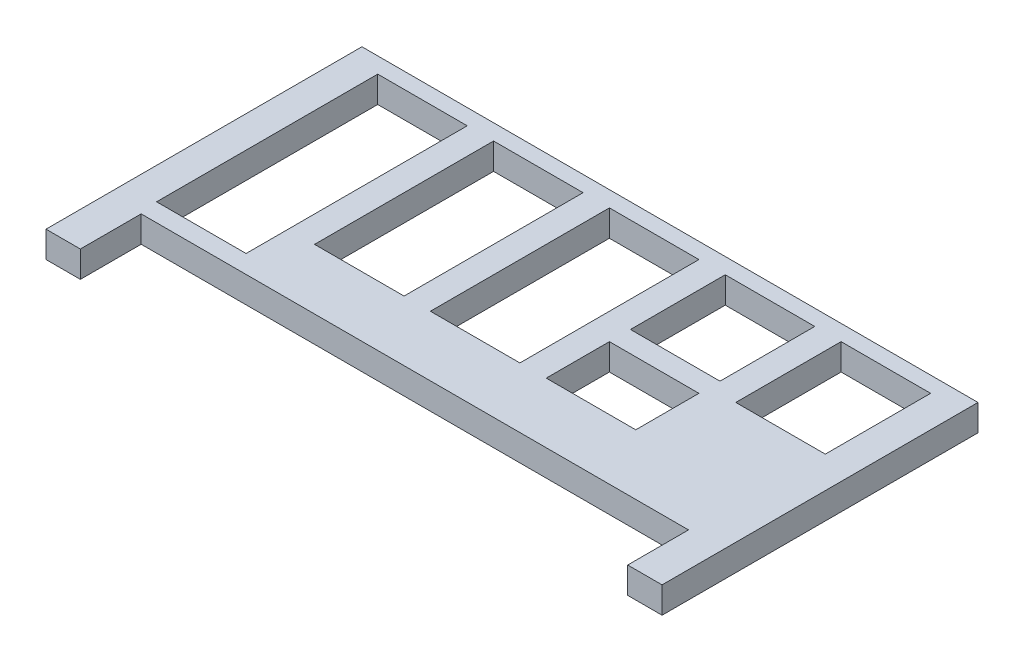
SolidWorks part; units mm, degrees
ref_plane "Front" through (0, 0, 0) normal (0, 0, 1) x (1, 0, 0)
ref_plane "Top" through (0, 0, 0) normal (0, 1, 0) x (1, 0, 0)
ref_plane "Right" through (0, 0, 0) normal (1, 0, 0) x (0, 0, -1)
sketch "Sketch1" plane through (0, 0, 0) normal (0, 1, 0) x (1, 0, 0)
  line L1 (-58.5, -30) -> (58.5, -30)
  line L2 (-58.5, -30) -> (-58.5, 30)
  line L3 (-58.5, 30) -> (58.5, 30)
  line L4 (58.5, -30) -> (58.5, 30)
  line L5 (-58.5, -30) -> (58.5, 30) construction
  line L6 (-58.5, 30) -> (58.5, -30) construction
  line L12 (13.5, 9) -> (30.5, 9)
  line L13 (-52.5, -15) -> (-35.5, -15)
  line L14 (-52.5, -15) -> (-52.5, 27)
  line L15 (-52.5, 27) -> (-35.5, 27)
  line L16 (-35.5, -15) -> (-35.5, 27)
  line L17 (-52.5, -15) -> (-35.5, 27) construction
  line L18 (-52.5, 27) -> (-35.5, -15) construction
  line L23 (13.5, 9) -> (13.5, 27)
  line L24 (13.5, 27) -> (30.5, 27)
  line L25 (-13.5, 27) -> (-30.5, 27)
  line L26 (-13.5, 27) -> (-13.5, -7)
  line L27 (-13.5, -7) -> (-30.5, -7)
  line L28 (-30.5, 27) -> (-30.5, -7)
  line L29 (-13.5, 27) -> (-30.5, -7) construction
  line L30 (-13.5, -7) -> (-30.5, 27) construction
  line L35 (30.5, 9) -> (30.5, 27)
  line L36 (13.5, 9) -> (30.5, 27) construction
  line L37 (-8.5, -7) -> (8.5, -7)
  line L38 (-8.5, -7) -> (-8.5, 27)
  line L39 (-8.5, 27) -> (8.5, 27)
  line L40 (8.5, -7) -> (8.5, 27)
  line L41 (-8.5, -7) -> (8.5, 27) construction
  line L42 (-8.5, 27) -> (8.5, -7) construction
  line L48 (13.5, 27) -> (30.5, 9) construction
  line L49 (35.5, 7) -> (52.5, 7)
  line L50 (35.5, 7) -> (35.5, 27)
  line L51 (35.5, 27) -> (52.5, 27)
  line L52 (52.5, 7) -> (52.5, 27)
  line L53 (35.5, 7) -> (52.5, 27) construction
  line L54 (35.5, 27) -> (52.5, 7) construction
  line L55 (13.5, 5) -> (30.5, 5)
  line L56 (13.5, 5) -> (13.5, -7)
  line L57 (13.5, -7) -> (30.5, -7)
  line L58 (30.5, 5) -> (30.5, -7)
  line L59 (13.5, 5) -> (30.5, -7) construction
  line L60 (13.5, -7) -> (30.5, 5) construction
  line L61 (51.975, -30) -> (58.5, -30)
  line L67 (-51.975, -30) -> (51.975, -30)
  line L68 (-51.975, -30) -> (-51.975, -18.45)
  line L69 (-51.975, -18.45) -> (51.975, -18.45)
  line L70 (51.975, -30) -> (51.975, -18.45)
  point P0 (0, 0)
  point P6 (44, 17)
  point P9 (22, 18)
  point P11 (-44, 6)
  point P21 (-22, 10)
  point P26 (22, -1)
  point P31 (0, 10)
  dimension "D1" = 117
  dimension "D2" = 60
  dimension "D3" = 6
  dimension "D4" = 3
  dimension "D5" = 17
  dimension "D6" = 5
  dimension "D7" = 17
  dimension "D8" = 3
  dimension "D9" = 5
  dimension "D10" = 3
  dimension "D11" = 17
  dimension "D12" = 5
  dimension "D13" = 17
  dimension "D14" = 18
  dimension "D15" = 5
  dimension "D16" = 17
  dimension "D17" = 20
  dimension "D18" = 12
  dimension "D19" = 6
  dimension "D20" = 6.525
  dimension "D21" = 42
  dimension "D22" = 34
  dimension "D23" = 4
  dimension "D25" = 34
  dimension "D26" = 11.55
  dimension "D27" = 103.95
extrude "Boss-Extrude1" add sketch "Sketch1" along normal blind 5
